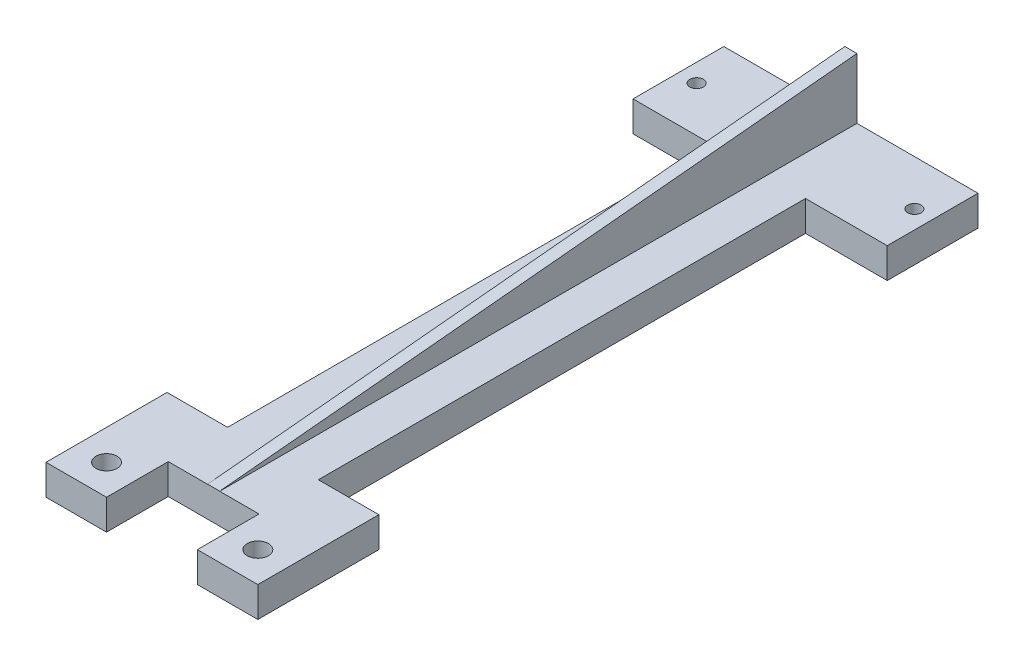
SolidWorks part; units mm, degrees
ref_plane "Front Plane" through (0, 0, 0) normal (0, 0, 1) x (1, 0, 0)
ref_plane "Top Plane" through (0, 0, 0) normal (0, 1, 0) x (1, 0, 0)
ref_plane "Right Plane" through (0, 0, 0) normal (1, 0, 0) x (0, 0, -1)
sketch "Sketch1" plane through (0, 0, 0) normal (0, 1, 0) x (1, 0, 0)
  line L1 (0, 0) -> (42, 0)
  line L2 (0, 0) -> (0, 15)
  line L3 (0, 15) -> (42, 15)
  line L4 (42, 0) -> (42, 15)
  dimension "D1" = 42
  dimension "D2" = 15
extrude "Boss-Extrude1" add sketch "Sketch1" along normal blind 5
sketch "Sketch2" plane through (0, 5, 0) normal (0, 1, 0) x (1, 0, 0)
  line L0 (3, 7.5) -> (39, 7.5) construction
  line L3 (21, 15) -> (21, 0) construction
  line L4 (42, 15) -> (0, 15) construction
  line L5 (0, 0) -> (42, 0) construction
  circle A0 centre (3, 7.5) radius 1.115
  circle A1 centre (39, 7.5) radius 1.115
  point P2 (21, 7.5)
  point P3 (21, 7.5)
  dimension "D2" = 2.23
  dimension "D1" = 36
extrude "Cut-Extrude1" cut sketch "Sketch2" against normal through all
sketch "Sketch3" plane through (0, 5, 0) normal (0, 1, 0) x (1, 0, 0)
  line L0 (0, 0) -> (42, 0) construction
  line L1 (13.5, 0) -> (28.5, 0)
  line L2 (13.5, 0) -> (13.5, -80.5)
  line L3 (13.5, -80.5) -> (28.5, -80.5)
  line L4 (28.5, 0) -> (28.5, -80.5)
  point P4 (21, 0)
  point P7 (21, 0)
  dimension "D1" = 15
  dimension "D2" = 80.5
extrude "Boss-Extrude2" add sketch "Sketch3" against normal up to surface (5 mm away) up to face at (3, 0, -6.385)
sketch "Sketch4" plane through (0, 5, 0) normal (0, 1, 0) x (1, 0, 0)
  line L0 (13.5, -80.5) -> (28.5, -80.5) construction
  line L1 (3.5, -80.5) -> (38.5, -80.5)
  line L2 (3.5, -80.5) -> (3.5, -90.5)
  line L3 (3.5, -90.5) -> (38.5, -90.5)
  line L4 (38.5, -80.5) -> (38.5, -90.5)
  point P4 (21, -80.5)
  point P7 (21, -80.5)
  dimension "D1" = 10
  dimension "D2" = 35
extrude "Boss-Extrude3" add sketch "Sketch4" against normal up to surface (5 mm away) up to face at (3, 0, -6.385)
sketch "Sketch5" plane through (0, 5, 0) normal (0, 1, 0) x (1, 0, 0)
  line L0 (3.5, -90.5) -> (13.5, -100.5) construction
  line L1 (3.5, -90.5) -> (13.5, -90.5)
  line L2 (3.5, -90.5) -> (3.5, -100.5)
  line L3 (3.5, -100.5) -> (13.5, -100.5)
  line L4 (13.5, -90.5) -> (13.5, -100.5)
  line L5 (38.5, -90.5) -> (28.5, -90.5)
  line L6 (38.5, -90.5) -> (38.5, -100.5)
  line L7 (38.5, -100.5) -> (28.5, -100.5)
  line L8 (28.5, -90.5) -> (28.5, -100.5)
  line L9 (28.5, -90.5) -> (38.5, -100.5) construction
  dimension "D1" = 10
  dimension "D2" = 10
extrude "Boss-Extrude4" add sketch "Sketch5" against normal up to surface (5 mm away) up to face at (3, 0, -6.385)
sketch "Sketch6" plane through (0, 5, 0) normal (0, 1, 0) x (1, 0, 0)
  line L0 (13.5, -100.5) -> (3.5, -90.5) construction
  line L1 (3.5, -80.5) -> (3.5, -100.5) construction
  line L2 (38.5, -100.5) -> (28.5, -90.5) construction
  line L3 (13.5, -90.5) -> (28.5, -90.5) construction
  circle A0 centre (8.5, -95.5) radius 1.75
  circle A1 centre (33.5, -95.5) radius 1.75
  dimension "D1" = 3.5
extrude "Cut-Extrude2" cut sketch "Sketch6" against normal through all
sketch "Sketch7" plane through (0, 5, 0) normal (0, 1, 0) x (1, 0, 0)
  line L2 (13.5, -90.3) -> (28.5, -90.3)
  line L3 (13.5, -90.3) -> (28.5, -90.3)
  line L6 (13.5, -90.3) -> (13.5, -90.5)
  line L7 (13.5, -90.5) -> (28.5, -90.5)
  line L8 (28.5, -90.5) -> (28.5, -90.3)
  dimension "D1" = 0.2
extrude "Cut-Extrude3" cut sketch "Sketch7" against normal through all
sketch "Sketch8" plane through (0, 5, 0) normal (0, 1, 0) x (1, 0, 0)
  line L0 (42, 15) -> (0, 15) construction
  line L1 (20, 15) -> (22, 15)
  line L2 (20, 15) -> (20, -90.3)
  line L3 (20, -90.3) -> (22, -90.3)
  line L4 (22, 15) -> (22, -90.3)
  line L5 (28.5, -90.3) -> (13.5, -90.3) construction
  point P8 (21, -90.3)
  point P9 (21, -90.3)
  dimension "D1" = 2
extrude "Boss-Extrude5" add sketch "Sketch8" along normal blind 10
sketch "Sketch9" plane through (20, 0, 0) normal (-1, 0, 0) x (0, 0, 1)
  line L0 (-15, 15) -> (90.5, 5)
  line L1 (80.5, 5) -> (100.5, 5) construction
  line L2 (90.5, 5) -> (90.3, 15)
  line L3 (90.3, 15) -> (-15, 15)
extrude "Cut-Extrude4" cut sketch "Sketch9" against normal through all
